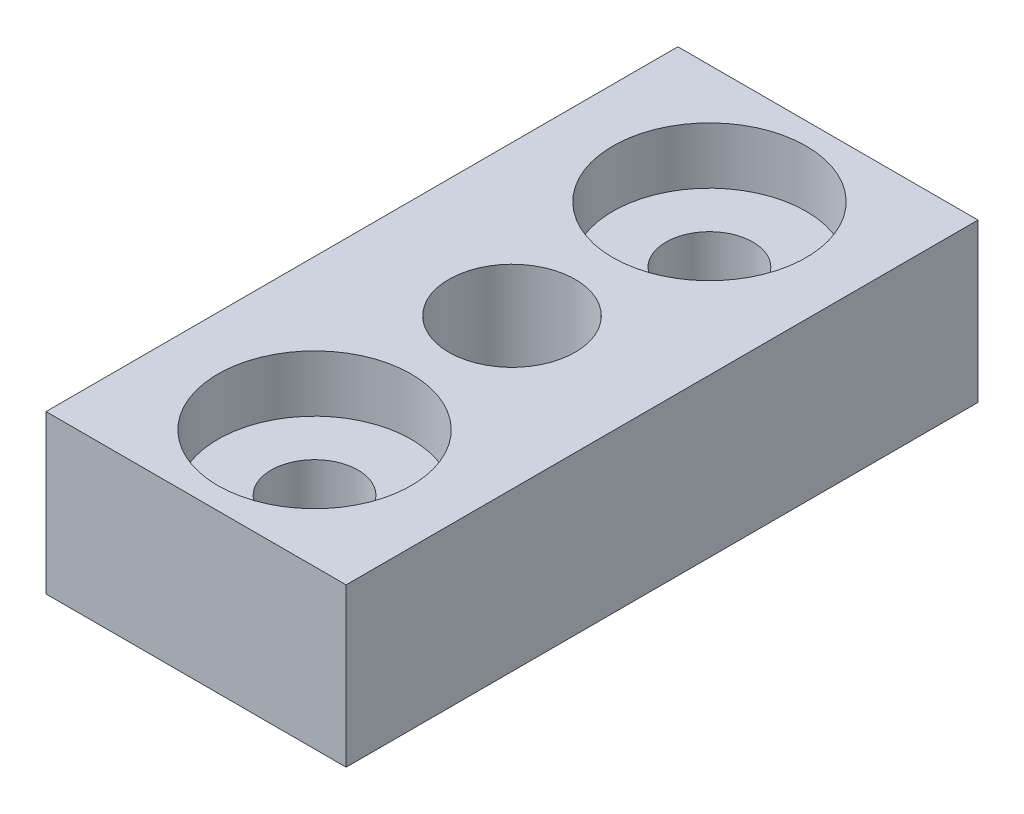
SolidWorks part; units mm, degrees
ref_plane "Front Plane" through (0, 0, 0) normal (0, 0, 1) x (1, 0, 0)
ref_plane "Top Plane" through (0, 0, 0) normal (0, 1, 0) x (1, 0, 0)
ref_plane "Right Plane" through (0, 0, 0) normal (1, 0, 0) x (0, 0, -1)
sketch "Sketch1" plane through (0, 0, 0) normal (0, 1, 0) x (1, 0, 0)
  line L1 (-9.5, 20) -> (9.5, 20)
  line L2 (-9.5, 20) -> (-9.5, -20)
  line L3 (-9.5, -20) -> (9.5, -20)
  line L4 (9.5, 20) -> (9.5, -20)
  circle A1 centre (0, 0) radius 4
  dimension "D1" = 9.5
  dimension "D2" = 8
  dimension "D3" = 40
  dimension "D4" = 19
  dimension "D5" = 20
extrude "Boss-Extrude1" add sketch "Sketch1" along normal blind 10
hole_wizard "CBORE for M5 Hex Head Bolt1" positions "Sketch2" profile "Sketch3" counterbore size "M5" standard "ANSI Metric" end condition up to next
sketch "Sketch2" plane through (0, 10, 0) normal (0, 1, 0) x (1, 0, 0)
  line L0 (9.5, 20) -> (-9.5, 20) construction
  line L1 (-9.5, -20) -> (9.5, -20) construction
  line L2 (9.5, -20) -> (9.5, 20) construction
  point P0 (0, 12.5)
  point P2 (0, -12.5)
  dimension "D1" = 7.5
  dimension "D2" = 7.5
  dimension "D3" = 9.5
  dimension "D4" = 9.5
sketch "Sketch3" plane through (0, 10, -12.5) normal (1, 0, 0) x (0, 0, 1)
  line L0 (0, 0) -> (0, 10)
  line L1 (0, 10) -> (2.75, 10)
  line L3 (2.75, 10) -> (2.75, 3.58)
  line L4 (2.75, 3.58) -> (6.12, 3.58)
  line L5 (6.12, 3.58) -> (6.12, 0)
  line L7 (6.12, 0) -> (0, 0)
  line L11 (0, -6.35) -> (0, 107.95) construction
  dimension "Thru Hole Dia." = 5.5
  dimension "Thru Hole Depth" = 10
  dimension "C'Bore Dia." = 12.24
  dimension "C'Bore Depth" = 3.58
